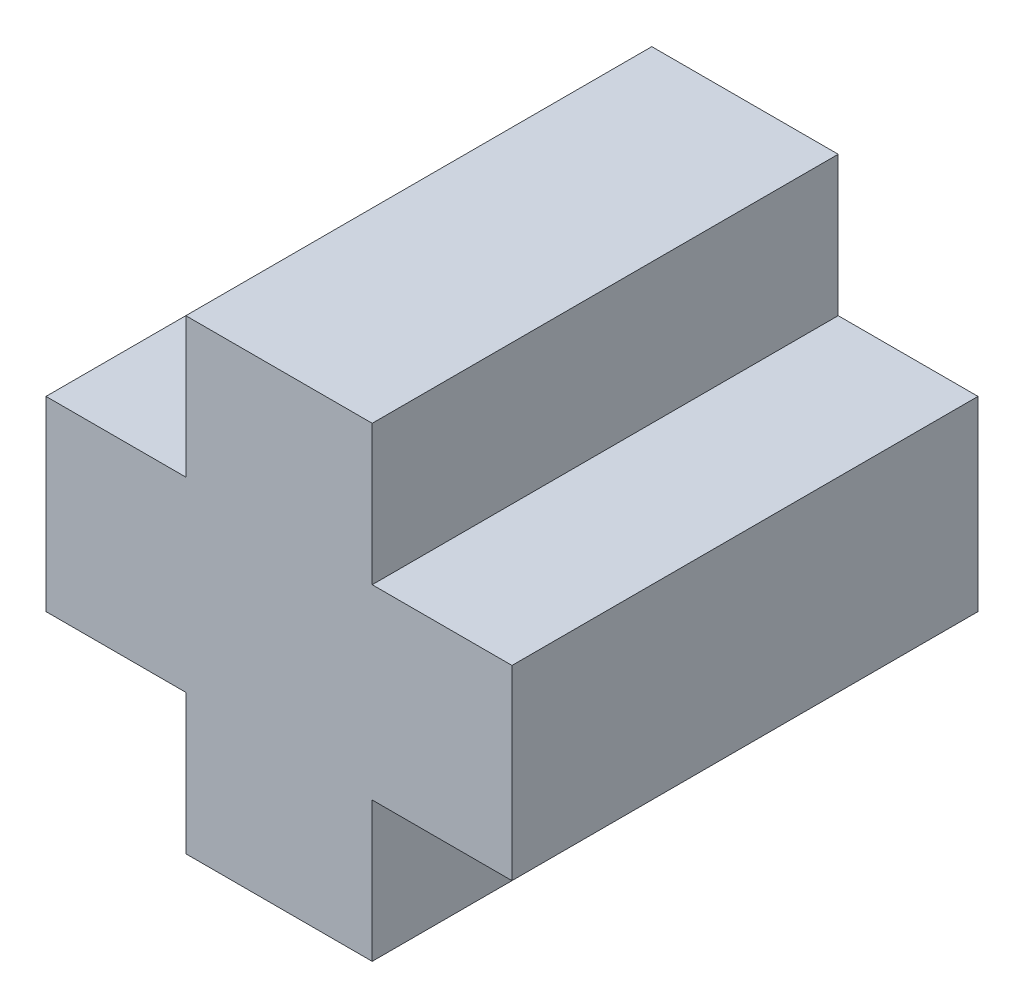
SolidWorks part; units mm, degrees
ref_plane "Front Plane" through (0, 0, 0) normal (0, 0, 1) x (1, 0, 0)
ref_plane "Top Plane" through (0, 0, 0) normal (0, 1, 0) x (1, 0, 0)
ref_plane "Right Plane" through (0, 0, 0) normal (1, 0, 0) x (0, 0, -1)
sketch "Sketch1" plane through (0, 0, 0) normal (0, 0, 1) x (1, 0, 0)
  line L0 (-5.9493, 6.5471) -> (-5.9493, 3.5471)
  line L1 (-5.9493, 3.5471) -> (-8.9493, 3.5471)
  line L2 (-8.9493, 3.5471) -> (-8.9493, -0.4529)
  line L3 (-8.9493, -0.4529) -> (-5.9493, -0.4529)
  line L4 (-5.9493, -0.4529) -> (-5.9493, -3.4529)
  line L5 (-5.9493, -3.4529) -> (-1.9493, -3.4529)
  line L6 (-1.9493, -3.4529) -> (-1.9493, -0.4529)
  line L7 (-1.9493, -0.4529) -> (1.0507, -0.4529)
  line L8 (1.0507, -0.4529) -> (1.0507, 3.5471)
  line L9 (1.0507, 3.5471) -> (-1.9493, 3.5471)
  line L10 (-1.9493, 3.5471) -> (-1.9493, 6.5471)
  line L11 (-1.9493, 6.5471) -> (-5.9493, 6.5471)
  dimension "D1" = 10
  dimension "D2" = 10
  dimension "D3" = 3
  dimension "D4" = 3
extrude "Boss-Extrude1" add sketch "Sketch1" along normal blind 10
